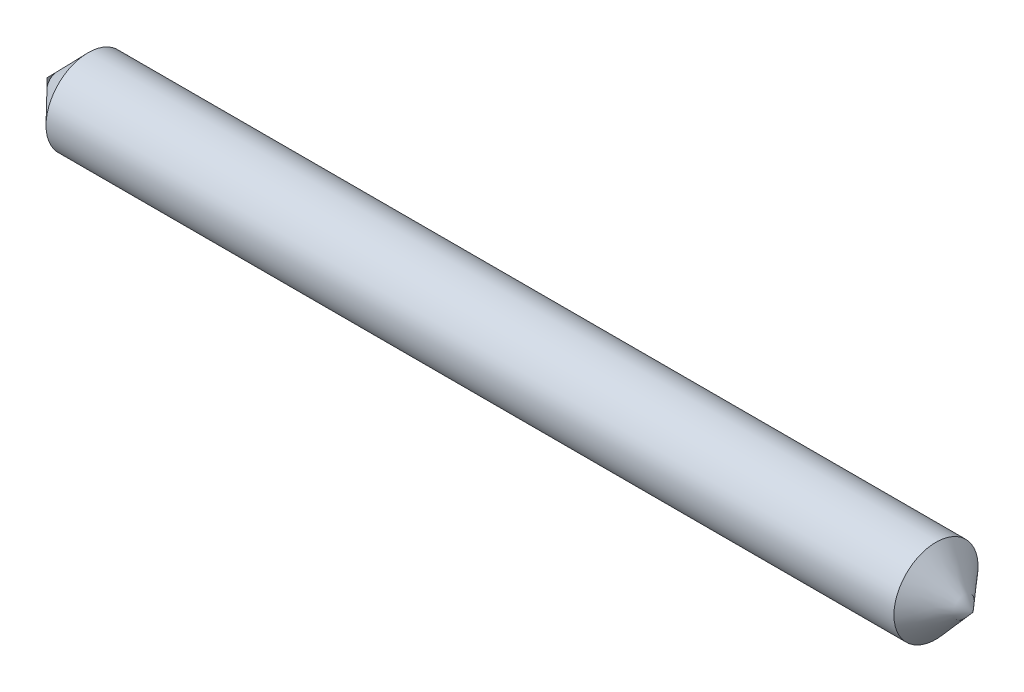
SolidWorks part; units mm, degrees
ref_plane "Alzado" through (0, 0, 0) normal (0, 0, 1) x (1, 0, 0)
ref_plane "Planta" through (0, 0, 0) normal (0, 1, 0) x (1, 0, 0)
ref_plane "Vista lateral" through (0, 0, 0) normal (1, 0, 0) x (0, 0, -1)
sketch "Croquis1" plane through (0, 0, 0) normal (0, 0, 1) x (1, 0, 0)
  line L0 (-79.0532, 7.1848) -> (320.9468, 7.1848)
  line L1 (320.9468, 7.1848) -> (304.9249, 25.3633)
  line L2 (304.9249, 25.3633) -> (-61.4093, 25.3633)
  line L3 (-61.4093, 25.3633) -> (-79.0532, 7.1848)
revolve "Revolución2" add sketch "Croquis1" angle 360 about L0
